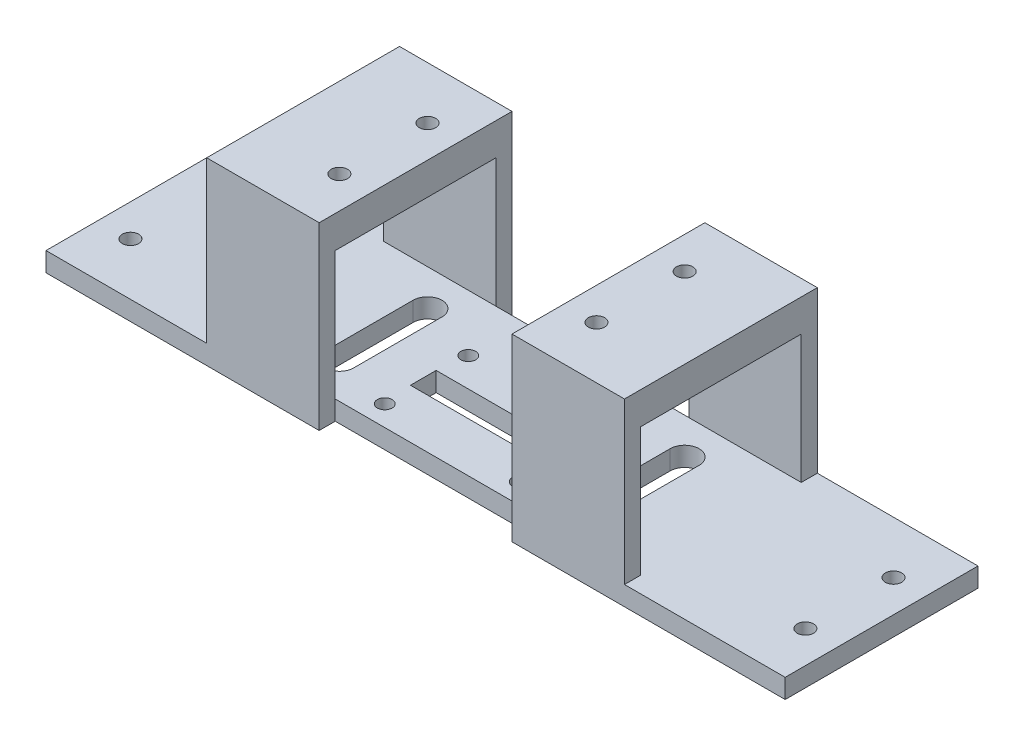
SolidWorks part; units mm, degrees
ref_plane "Front Plane" through (0, 0, 0) normal (0, 0, 1) x (1, 0, 0)
ref_plane "Top Plane" through (0, 0, 0) normal (0, 1, 0) x (1, 0, 0)
ref_plane "Right Plane" through (0, 0, 0) normal (1, 0, 0) x (0, 0, -1)
sketch "Sketch1" plane through (0, 0, 0) normal (0, 1, 0) x (1, 0, 0)
  line L0 (0, -12.5) -> (0, 12.5)
  line L1 (0, -2.8) -> (-30, -2.8) construction
  line L2 (-25.5, 12.5) -> (-4.5, 12.5) construction
  line L3 (-4.5, -9.3) -> (-4.5, 3.7) construction
  line L4 (-25.5, -9.3) -> (-25.5, 3.7)
  line L5 (0, 12.5) -> (-30, 12.5)
  line L6 (-30, 12.5) -> (-30, -12.5)
  line L7 (-30, -12.5) -> (0, -12.5)
  line L8 (-4, -0.8) -> (-4, -4.8)
  line L13 (-26, -4.8) -> (-4, -4.8)
  line L14 (-4, -0.8) -> (-26, -0.8)
  line L15 (-26, -0.8) -> (-26, -4.8)
  circle A0 centre (-4.5, 3.7) radius 1.15
  circle A1 centre (-4.5, -9.3) radius 1.15
  circle A2 centre (-25.5, 3.7) radius 1.15
  circle A3 centre (-25.5, -9.3) radius 1.15
  point P4 (0, 0)
  point P6 (-15, -2.8)
  point P9 (-15, 12.5)
  point P13 (-4.5, -2.8)
  point P18 (-25.5, -2.8)
  point P20 (-15, -2.8)
  point P30 (-4, -2.8)
  point P33 (-26, -2.8)
  dimension "D6" = 2.3
  dimension "D7" = 2.3
  dimension "D8" = 2.3
  dimension "D9" = 2.3
  dimension "D1" = 25
  dimension "D2" = 30
  dimension "D3" = 21
  dimension "D4" = 0
  dimension "D5" = 13
  dimension "D10" = 8.8
  dimension "D12" = 13
  dimension "D13" = 4
  dimension "D14" = 0.5
  dimension "D15" = 0.5
extrude "Boss-Extrude1" add sketch "Sketch1" along normal blind 3
sketch "Sketch2" plane through (0, 3, 0) normal (0, 1, 0) x (1, 0, 0)
  line L0 (5, -5.588) -> (5, 5.588) construction
  line L1 (0, -12.5) -> (0, 12.5) construction
  line L2 (0, 10) -> (7.5, 10)
  line L3 (0, 10) -> (0, -10)
  line L4 (0, -10) -> (7.5, -10)
  line L5 (7.5, 10) -> (7.5, -10)
  line L6 (-30, 12.5) -> (-30, -12.5) construction
  line L7 (-30, 10) -> (-37.5, 10)
  line L8 (-30, 10) -> (-30, -10)
  line L9 (-30, -10) -> (-37.5, -10)
  line L10 (-37.5, 10) -> (-37.5, -10)
  circle A0 centre (5, 6.858) radius 1.27
  circle A1 centre (5, -6.858) radius 1.27
  circle A2 centre (-35, 6.858) radius 1.27
  circle A3 centre (-35, -6.858) radius 1.27
  point P3 (5, 0)
  dimension "D3" = 2.54
  dimension "D5" = 2.54
  dimension "D14" = 2.54
  dimension "D15" = 2.54
  dimension "D16" = 5
  dimension "D17" = 5
  dimension "D18" = 0
  dimension "D19" = 0
  dimension "D1" = 11.176
  dimension "D2" = 0
  dimension "D4" = 1.27
  dimension "D6" = 1.27
  dimension "D7" = 10
  dimension "D8" = 20
  dimension "D9" = 7.5
  dimension "D10" = 7.5
  dimension "D11" = 0
  dimension "D12" = 0
  dimension "D13" = 5
extrude "Boss-Extrude2" add sketch "Sketch2" against normal up to surface (3 mm away) up to face at (-15, 0, 2.8)
sketch "Sketch6" plane through (-37.5, 0, 0) normal (-1, 0, 0) x (0, 0, 1)
  line L1 (10, 3) -> (-10, 3)
  line L2 (10, 3) -> (10, 0)
  line L3 (10, 0) -> (-10, 0)
  line L4 (-10, 3) -> (-10, 0)
extrude "Boss-Extrude3" add sketch "Sketch6" along normal blind 10
sketch "Sketch7" plane through (7.5, 0, 0) normal (1, 0, 0) x (0, 0, -1)
  line L1 (-10, 3) -> (10, 3)
  line L2 (-10, 3) -> (-10, 0)
  line L3 (-10, 0) -> (10, 0)
  line L4 (10, 3) -> (10, 0)
extrude "Boss-Extrude4" add sketch "Sketch7" along normal blind 10
sketch "Sketch8" plane through (0, 3, 0) normal (0, 1, 0) x (1, 0, 0)
  line L1 (0, 10) -> (17.5, 10)
  line L2 (0, 10) -> (0, -10)
  line L3 (0, -10) -> (17.5, -10)
  line L4 (17.5, 10) -> (17.5, -10)
  line L5 (-30, 10) -> (-47.5, 10)
  line L6 (-30, 10) -> (-30, -10)
  line L7 (-30, -10) -> (-47.5, -10)
  line L8 (-47.5, 10) -> (-47.5, -10)
  circle A0 centre (5, 6.858) radius 1.27
  circle A1 centre (5, -6.858) radius 1.27
  circle A2 centre (-35, -6.858) radius 1.27
  circle A3 centre (-35, 6.858) radius 1.27
extrude "Boss-Extrude5" add sketch "Sketch8" along normal blind 25
sketch "Sketch13" plane through (0, 0, -10) normal (0, 0, -1) x (-1, 0, 0)
  line L1 (30, 28) -> (47.5, 28)
  line L2 (30, 28) -> (30, 0)
  line L3 (30, 0) -> (47.5, 0)
  line L4 (47.5, 28) -> (47.5, 0)
  line L5 (-17.5, 28) -> (0, 28)
  line L6 (-17.5, 28) -> (-17.5, 0)
  line L7 (-17.5, 0) -> (0, 0)
  line L8 (0, 28) -> (0, 0)
extrude "Boss-Extrude6" add sketch "Sketch13" along normal blind 5
sketch "Sketch14" plane through (0, 0, 10) normal (0, 0, 1) x (1, 0, 0)
  line L1 (0, 28) -> (17.5, 28)
  line L2 (0, 28) -> (0, 0)
  line L3 (0, 0) -> (17.5, 0)
  line L4 (17.5, 28) -> (17.5, 0)
  line L5 (-47.5, 28) -> (-30, 28)
  line L6 (-47.5, 28) -> (-47.5, 0)
  line L7 (-47.5, 0) -> (-30, 0)
  line L8 (-30, 28) -> (-30, 0)
extrude "Boss-Extrude7" add sketch "Sketch14" along normal blind 5
sketch "Sketch15" plane through (-30, 0, 0) normal (1, 0, 0) x (0, 0, -1)
  line L1 (-12.5, 3) -> (12.5, 3)
  line L2 (-12.5, 3) -> (-12.5, 23)
  line L3 (-12.5, 23) -> (12.5, 23)
  line L4 (12.5, 3) -> (12.5, 23)
  line L5 (-15, 28) -> (15, 28) construction
  dimension "D1" = 0
  dimension "D2" = 5
extrude "Cut-Extrude2" cut sketch "Sketch15" along normal through all both and the other way through all
sketch "Sketch16" plane through (-47.5, 0, 0) normal (-1, 0, 0) x (0, 0, 1)
  line L0 (15, 28) -> (15, 0) construction
  line L1 (-15, 0) -> (15, 0)
  line L2 (-15, 0) -> (-15, 3)
  line L3 (-15, 3) -> (15, 3)
  line L4 (15, 0) -> (15, 3)
  line L5 (12.5, 3) -> (-12.5, 3) construction
  dimension "D1" = 0
extrude "Boss-Extrude8" add sketch "Sketch16" along normal blind 25
sketch "Sketch19" plane through (17.5, 0, 0) normal (1, 0, 0) x (0, 0, -1)
  line L0 (15, 28) -> (15, 0) construction
  line L1 (-15, 0) -> (15, 0)
  line L2 (-15, 0) -> (-15, 3)
  line L3 (-15, 3) -> (15, 3)
  line L4 (15, 0) -> (15, 3)
  line L5 (-12.5, 3) -> (12.5, 3) construction
  dimension "D1" = 0
extrude "Boss-Extrude9" add sketch "Sketch19" along normal blind 25
hole_wizard "1/16 (0.0625) Press Dowel Hole1" positions "Sketch17" profile "Sketch18" hole size "1/16" standard "ANSI Inch" end condition through all
sketch "Sketch17" plane through (0, 3, 0) normal (0, 1, 0) x (1, 0, 0)
  line L0 (-72.5, -15) -> (-72.5, 15) construction
  line L1 (42.5, 15) -> (42.5, -15) construction
  circle A0 centre (-35, -6.858) radius 1.27 construction
  circle A1 centre (5, -6.858) radius 1.27 construction
  circle A2 centre (5, 6.858) radius 1.27 construction
  point P0 (-67.5, 6.858)
  point P2 (-67.5, -6.858)
  point P9 (37.5, -6.858)
  point P11 (37.5, 6.858)
  dimension "D1" = 5
  dimension "D2" = 5
  dimension "D3" = 0
  dimension "D4" = 0
  dimension "D5" = 5
  dimension "D6" = 5
  dimension "D7" = 0
sketch "Sketch18" plane through (-67.5, 3, -6.858) normal (1, 0, 0) x (0, 0, 1)
  line L0 (0, 0) -> (0, 3)
  line L1 (0, 3) -> (1.27, 3)
  line L2 (1.27, 3) -> (1.27, 0)
  line L5 (1.27, 0) -> (0, 0)
  line L11 (0, -6.35) -> (0, 107.95) construction
  dimension "Thru Hole Dia." = 2.54
  dimension "Thru Hole Depth" = 3
sketch "Sketch21" plane through (0, 3, 0) normal (0, 1, 0) x (1, 0, 0)
  line L0 (5, -6.858) -> (5, 6.858) construction
  line L1 (2.75, -6.858) -> (2.75, 6.858)
  line L2 (7.25, -6.858) -> (7.25, 6.858)
  line L3 (-35, 6.858) -> (-35, -6.858) construction
  line L4 (-32.75, 6.858) -> (-32.75, -6.858)
  line L5 (-37.25, 6.858) -> (-37.25, -6.858)
  arc A0 (2.75, -6.858) -> (7.25, -6.858) centre (5, -6.858) ccw
  arc A1 (7.25, 6.858) -> (2.75, 6.858) centre (5, 6.858) ccw
  arc A3 (-32.75, 6.858) -> (-37.25, 6.858) centre (-35, 6.858) ccw
  arc A4 (-37.25, -6.858) -> (-32.75, -6.858) centre (-35, -6.858) ccw
  point P4 (5, 0)
  point P9 (-35, 0)
  dimension "D1" = 2.25
  dimension "D2" = 4.5
extrude "Cut-Extrude3" cut sketch "Sketch21" against normal through all
